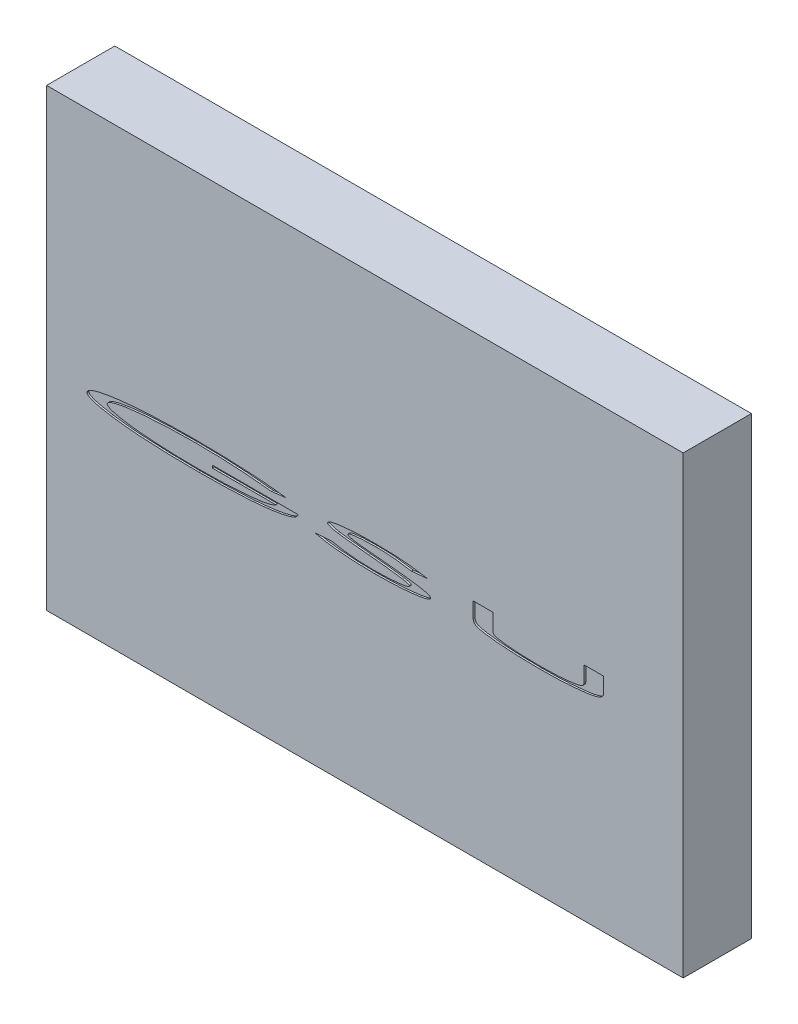
SolidWorks part; units mm, degrees
ref_plane "Front Plane" through (0, 0, 0) normal (0, 0, 1) x (1, 0, 0)
ref_plane "Top Plane" through (0, 0, 0) normal (0, 1, 0) x (1, 0, 0)
ref_plane "Right Plane" through (0, 0, 0) normal (1, 0, 0) x (0, 0, -1)
sketch "Sketch1" plane through (0, 0, 0) normal (0, 0, 1) x (1, 0, 0)
  line L1 (0, 0) -> (88.9, 0)
  line L2 (0, 0) -> (0, 63.5)
  line L3 (0, 63.5) -> (88.9, 63.5)
  line L4 (88.9, 0) -> (88.9, 63.5)
  dimension "D1" = 63.5
  dimension "D2" = 88.9
extrude "Boss-Extrude1" add sketch "Sketch1" along normal blind 9.525
sketch "Sketch2" plane through (0, 0, 9.525) normal (0, 0, 1) x (1, 0, 0)
  text T0 "GSU" font "Century Gothic" height 3.5
  point P1 (3.4792, 27.4482)
extrude "Cut-Extrude1" cut sketch "Sketch2" against normal blind 0.254
sketch "Sketch3" plane through (0, 0, 0) normal (-1, 0, 0) x (0, 0, 1)
  line L0 (0, 63.5) -> (0, 0) construction
  line L1 (0, 20.32) -> (3.175, 20.32)
  line L2 (0, 20.32) -> (0, 12.2006)
  line L3 (0, 12.2006) -> (3.175, 12.2006)
  line L4 (3.175, 20.32) -> (3.175, 12.2006)
  line L5 (9.525, 0) -> (0, 0) construction
  dimension "D1" = 20.32
  dimension "D2" = 3.175
extrude "Boss-Extrude2" add sketch "Sketch3" along normal blind 2.54
